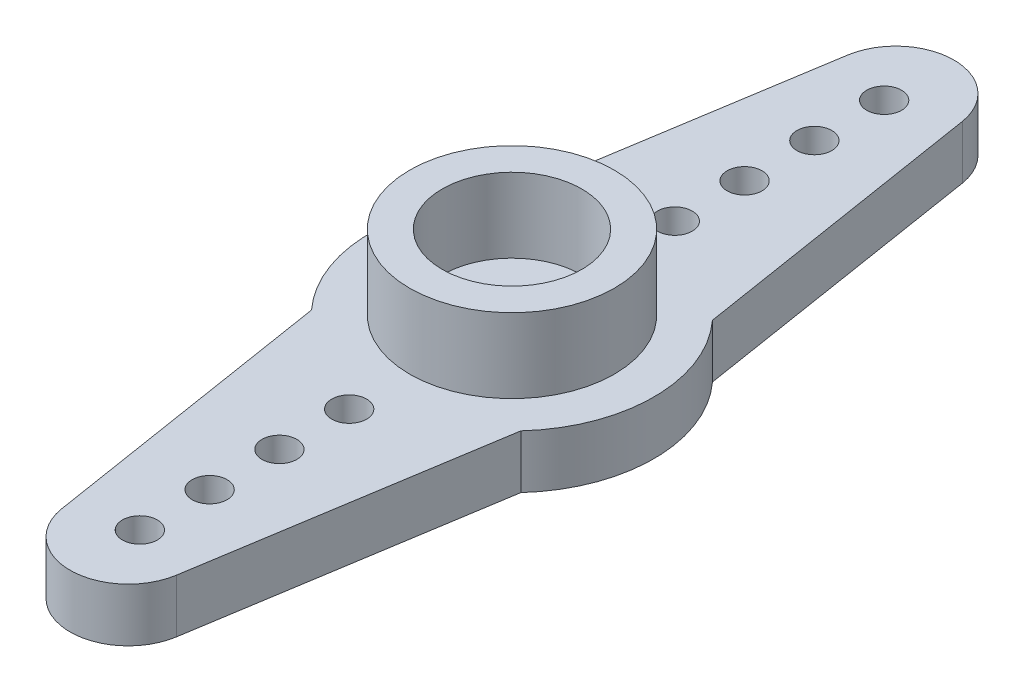
SolidWorks part; units mm, degrees
ref_plane "前视基准面" through (0, 0, 0) normal (0, 0, 1) x (1, 0, 0)
ref_plane "上视基准面" through (0, 0, 0) normal (0, 1, 0) x (1, 0, 0)
ref_plane "右视基准面" through (0, 0, 0) normal (1, 0, 0) x (0, 0, -1)
sketch "Sketch1" plane through (0, 0, 0) normal (0, 1, 0) x (1, 0, 0)
  circle A0 centre (0, 0) radius 6.1
  circle A1 centre (0, 0) radius 1.5
  dimension "D1" = 12.2
  dimension "D2" = 3
extrude "Boss-Extrude1" add sketch "Sketch1" along normal blind 2.3
sketch "Sketch2" plane through (0, 2.3, 0) normal (0, 1, 0) x (1, 0, 0)
  circle A0 centre (0, 0) radius 4.4
  circle A1 centre (0, 0) radius 3
  dimension "D1" = 8.8
  dimension "D2" = 6
extrude "Boss-Extrude2" add sketch "Sketch2" along normal blind 3.2
sketch "Sketch3" plane through (0, 0, 0) normal (0, -1, 0) x (1, 0, 0)
  line L0 (0, 0) -> (0, -19) construction
  line L1 (-2.469, -16.8925) -> (-4.5, -4.1183)
  line L2 (2.469, -16.8925) -> (4.5, -4.1183)
  arc A0 (-2.469, -16.8925) -> (2.469, -16.8925) centre (0, -16.5) ccw
  circle A1 centre (0, 0) radius 6.1 construction
  circle A2 centre (0, 0) radius 6.1
  circle A3 centre (0, -7) radius 0.75
  circle A4 centre (0, -10) radius 0.75
  circle A5 centre (0, -13) radius 0.75
  circle A6 centre (0, -16) radius 0.75
  circle A7 centre (0, 0) radius 1.5 construction
  point P12 (-6.1, 0)
  circle M3 centre (0, 0) radius 6.1
  dimension "D2" = 2.5
  dimension "D4" = 1.5
  dimension "D5" = 3
  dimension "D6" = 3
  dimension "D7" = 3
  dimension "D8" = 7
  dimension "D1" = 19
  dimension "D3" = 1.6
extrude "Boss-Extrude3" add sketch "Sketch3" against normal blind 2.3 contours A2 L0 A3 A4 A5 A6 A0 L2 | L0 L1 A0 A6 A5 A4 A3 M3
pattern_circular "CirPattern1" count 2 over 360 about axis through (0, 0, 0) along (0, 1, 0) of "Boss-Extrude3"
